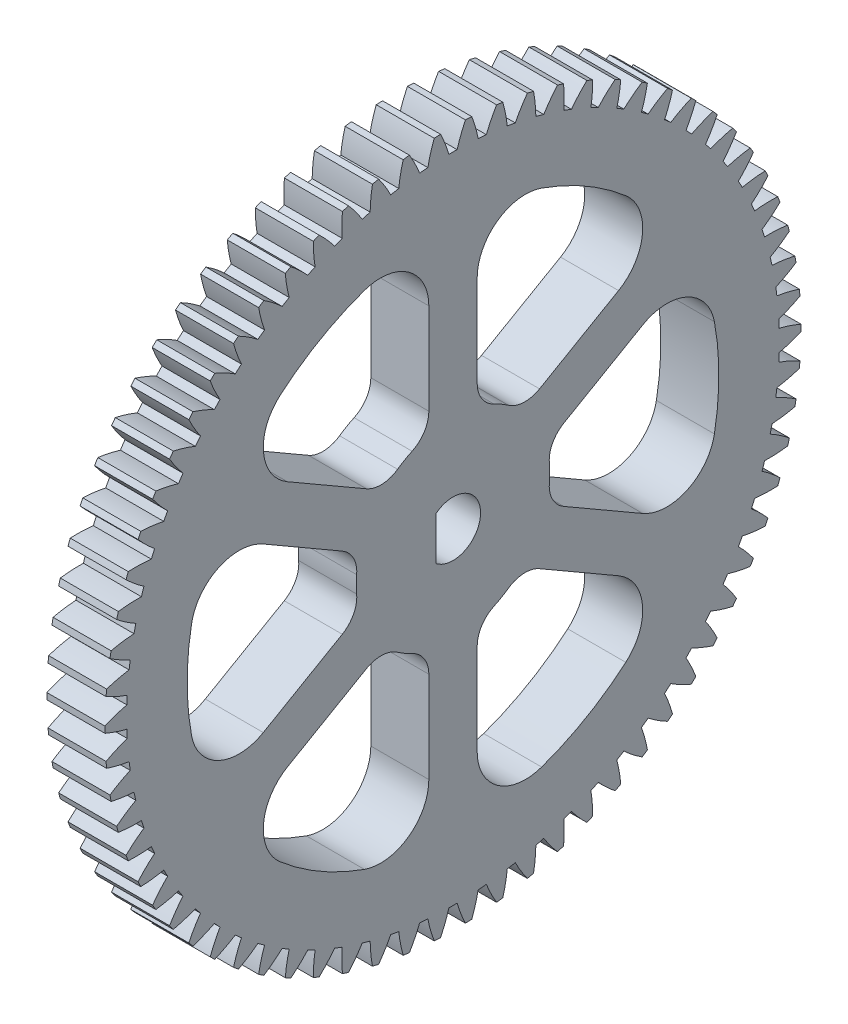
SolidWorks part; units mm, degrees
ref_plane "Plane1" through (0, 0, 0) normal (0, 0, 1) x (1, 0, 0)
ref_plane "Plane2" through (0, 0, 0) normal (0, 1, 0) x (1, 0, 0)
ref_plane "Plane3" through (0, 0, 0) normal (1, 0, 0) x (0, 0, -1)
sketch "HoldingSke" plane through (0, 0, 0) normal (0, 1, 0) x (1, 0, 0)
  line L0 (0, 0) -> (0.342, -0.9397)
  line L1 (-15, 0) -> (100, 0) construction
  line L2 (0, 0) -> (-2.1039, 2.3779)
  line L3 (0, 0) -> (-11.863, 4.5341)
  line L4 (0, 0) -> (2.9537, 8.1152)
  line L5 (0, 0) -> (-46.8476, -17.4728)
  line L6 (0, 0) -> (-4.9738, -3.3558)
  line L7 (-2.1039, 2.3779) -> (8.6587, 51.2065)
  line L8 (-76.2, 54.61) -> (-75.2, 54.61)
  line L9 (-71.009, 38.7566) -> (-53.1078, 45.2721)
  line L10 (-76.2, 71.12) -> (104.1128, 71.12)
  line L11 (0, 0) -> (-6, 0)
  line L12 (-76.2, 101.6) -> (-76.162, 101.6)
  line L13 (24.9733, 27.94) -> (52.9518, 28.4284)
  line L14 (24.9733, 27.94) -> (24.9743, 27.94)
  line L15 (24.9733, 27.94) -> (100.4006, 29.5858)
  line L16 (-63.627, -1) -> (-12.827, -1)
  circle A0 centre (0, 0) radius 3
  circle A1 centre (0, 0) radius 33.749
  circle A2 centre (0, 0) radius 37.5
  circle A3 centre (0, 0) radius 3
  dimension "MHD" = 67.498
  dimension "Hub_dia" = 75
  dimension "Bore" = 6
  dimension "MBD" = 6
  dimension "Num_teeth" = 70
  dimension "Pitch" = 1
  dimension "Overall_len" = 50
  dimension "Show_teeth" = 70
  dimension "Thickness" = 6
  dimension "OAL" = 50.0007
  dimension "T_dim" = 1
  dimension "Ap" = 20
  dimension "H" = 19.05
  dimension "Pitch_radius" = 180.3128
  dimension "Width" = 6
  dimension "Backlash" = 0.038
  dimension "Addendum_fac" = 1
  dimension "Dedendum_fac" = 1.25
  dimension "Clearance_fac" = 0.25
  dimension "Dedendum_add" = 0.001
  dimension "Module" = 1
sketch "BasProSke" plane through (0, 0, 0) normal (0, 1, 0) x (1, 0, 0)
  line L0 (-10, 0) -> (60, 0) construction
  line L1 (0, 0) -> (0, 36)
  line L2 (0, 0) -> (6, 0)
  line L3 (6, 0) -> (6, 36)
  line L4 (6, 36) -> (0, 36)
  dimension "Thickness" = 6
  dimension "Diameter" = 72
revolve "Base-Revolve" add sketch "BasProSke" angle 360 about L0
sketch "TooCutSke" plane through (0, 0, 0) normal (1, 0, 0) x (0, 0, -1)
  line L1 (0, 0) -> (0, 107) construction
  line L2 (0, 0) -> (-0.8518, 34.9896) construction
  line L3 (0, 0) -> (-3.1399, 69.9148) construction
  line L4 (-0.8518, 34.9896) -> (-1.5699, 34.9574) construction
  arc A0 (0.4247, 33.7463) -> (-0.4247, 33.7463) centre (0, 0) ccw
  arc A1 (1.3008, 36.0019) -> (-1.3008, 36.0019) centre (0, 0) ccw
  circle A2 centre (0, 0) radius 35 construction
  circle A3 centre (0, 0) radius 32.8892 construction
  arc A4 (-0.4247, 33.7463) -> (-1.3008, 36.0019) centre (-13.8641, 29.8243) ccw
  arc A5 (1.3008, 36.0019) -> (0.4247, 33.7463) centre (13.8641, 29.8243) ccw
  dimension "Root_dia" = 67.498
  dimension "Overcut_dia" = 72.0508
  dimension "Pitch_dia" = 70
  dimension "Base_dia" = 65.7785
  dimension "Flank_rad" = 14
  dimension "Half_ang" = 2.571
  dimension "Half_CT" = 0.7188
extrude "ToothCut" cut sketch "TooCutSke" along normal through all
fillet "Breaks" [suppressed] radius 0.02
fillet "RootFillets" [suppressed] radius 0.251
pattern_circular "TeethCuts" count 70 every 5.143 about axis through (-10, 0, 0) along (1, 0, 0) of "ToothCut", "RootFillets", "Breaks"
sketch "HubNeaOneSke" plane through (0, 0, 0) normal (-1, 0, 0) x (0, 0, 1)
  circle A0 centre (0, 0) radius 33.749
  dimension "Diameter" = 67.498
extrude "HubNearOne" [suppressed] add sketch "HubNeaOneSke" along normal blind 44.0007
sketch "HubNeaBotSke" plane through (0, 0, 0) normal (-1, 0, 0) x (0, 0, 1)
  circle A0 centre (0, 0) radius 33.749
  dimension "Diameter" = 67.498
extrude "HubNearBoth" [suppressed] add sketch "HubNeaBotSke" along normal blind 22.0004
ref_plane "FarPln" through (6, 0, 0) normal (1, 0, 0) x (0, 0, -1)
sketch "HubFarSke" plane through (6, 0, 0) normal (1, 0, 0) x (0, 0, -1)
  circle A0 centre (0, 0) radius 33.749
  dimension "Diameter" = 67.498
extrude "HubFar" [suppressed] add sketch "HubFarSke" along normal blind 22.0004
sketch "KeySke" plane through (0, 0, 0) normal (1, 0, 0) x (0, 0, -1)
  line L0 (-1, 0) -> (-1, 4)
  line L1 (-1, 4) -> (1, 4)
  line L2 (1, 4) -> (1, 0)
  line L3 (0, 0) -> (0, 34) construction
  line L4 (-1, 0) -> (1, 0)
  dimension "Offset" = 4
  dimension "Width" = 2
extrude "Keyway" [suppressed] cut sketch "KeySke" along normal mid plane 100.0014
pattern_circular "Keyway2" [suppressed] count 2 every 90 about axis through (-10, 0, 0) along (1, 0, 0)
sketch "Sketch1" plane through (6, 0, 0) normal (1, 0, 0) x (0, 0, -1)
  line L0 (-1.7493, 2.25) -> (-1.7493, -2.25)
  arc A0 (-1.7493, -2.25) -> (-1.7493, 2.25) centre (0, 0) ccw
  dimension "D1" = 5.7
  dimension "D2" = 4.5
extrude "Cut-Extrude1" cut sketch "Sketch1" against normal through all
sketch "Sketch2" plane through (6, 0, 0) normal (1, 0, 0) x (0, 0, -1)
  line L0 (-2.5, 27.3861) -> (-2.5, 9.6825)
  line L1 (-7.1353, 7.0063) -> (-22.4671, 15.8581)
  arc A1 (-2.5, 9.6825) -> (-7.1353, 7.0063) centre (0, 0) ccw
  arc A2 (-2.5, 27.3861) -> (-22.4671, 15.8581) centre (0, 0) ccw
  dimension "D2" = 20
  dimension "D3" = 55
  dimension "D4" = 2.5
  dimension "D5" = 2.5
  dimension "D6" = 60
extrude "Cut-Extrude2" cut sketch "Sketch2" against normal through all
fillet "Fillet1" radius 5 2 edges at (3, 15.8581, 22.4671) (3, 27.3861, 2.5)
fillet "Fillet2" radius 3 2 edges at (3, 7.0063, 7.1353) (3, 9.6825, 2.5)
pattern_circular "CirPattern1" count 6 every 60 about axis through (0, 0, 0) along (1, 0, 0) of "Fillet1", "Cut-Extrude2", "Fillet2"
equation "' \"Module@HoldingSke\" = 6.35"
equation "' \"Num_teeth@HoldingSke\" = 12"
equation "' \"Ap@HoldingSke\" =  20"
equation "' \"Ap@HoldingSke\" = 20"
equation "' \"Width@HoldingSke\" = 0.5 * 25.4"
equation "' \"Hub_dia@HoldingSke\"= 1 * 25.4"
equation "' \"Hub_dia@HoldingSke\" = 1 * 25.4"
equation "' \"Overall_len@HoldingSke\" = 1.0 * 25.4"
equation "' \"Bore@HoldingSke\" = 0.75 * 25.4"
equation "' \"T_dim@HoldingSke\" = 0.1 * 25.4"
equation "' \"Width@KeySke\" = 0.25 * 25.4"
equation "' \"Show_teeth@HoldingSke\" = 13"
equation "' \"Backlash@HoldingSke\" = 0.009 * 25.4"
equation "' \"Addendum_fac@HoldingSke\" = 1.0"
equation "' \"Dedendum_fac@HoldingSke\" = 1.25"
equation "' \"Dedendum_add@HoldingSke\" = 0.00005 * 25.4"
equation "' \"Clearance_fac@HoldingSke\" = 0.25"
equation "\"Pitch@HoldingSke\" = 1 / \"Module@HoldingSke\""
equation "\"Overcut_dia@TooCutSke\" = (\"Num_teeth@HoldingSke\" + 2 * \"Addendum_fac@HoldingSke\") / \"Pitch@HoldingSke\" + 0.002 * 25.4"
equation "\"Pitch_dia@TooCutSke\" = \"Num_teeth@HoldingSke\" / \"Pitch@HoldingSke\""
equation "\"Base_dia@TooCutSke\" = \"Num_teeth@HoldingSke\" / \"Pitch@HoldingSke\" * cos((\"Ap@HoldingSke\"  * 3.14159265 / 180))"
equation "\"Root_dia@TooCutSke\" = (\"Num_teeth@HoldingSke\" + 2) / \"Pitch@HoldingSke\" - 2 * (\"Addendum_fac@HoldingSke\" + \"Dedendum_fac@HoldingSke\") / \"Pitch@HoldingSke\" - \"Dedendum_add@HoldingSke\" * 2"
equation "\"Half_ang@TooCutSke\" = 180 / \"Num_teeth@HoldingSke\""
equation "\"Half_CT@TooCutSke\" = \"Num_teeth@HoldingSke\" / \"Pitch@HoldingSke\" * sin((3.14159265 / 2 / \"Num_teeth@HoldingSke\")) / 2 - 7 * \"Backlash@HoldingSke\" / 4"
equation "\"Flank_rad@TooCutSke\" = \"Num_teeth@HoldingSke\" / \"Pitch@HoldingSke\" / 5"
equation "\"Radius@RootFillets\" = \"Clearance_fac@HoldingSke\" / \"Pitch@HoldingSke\" + \"Dedendum_add@HoldingSke\""
equation "\"Break_rad@Breaks\" = 0.02 / \"Pitch@HoldingSke\""
equation "\"Thickness@HoldingSke\" = \"Width@HoldingSke\""
equation "\"OAL@HoldingSke\" = \"Thickness@HoldingSke\""
equation "\"MHD@HoldingSke\" = (\"Num_teeth@HoldingSke\" + 2) / \"Pitch@HoldingSke\" - 2 * (\"Addendum_fac@HoldingSke\" + \"Dedendum_fac@HoldingSke\")  / \"Pitch@HoldingSke\" - \"Dedendum_add@HoldingSke\" * 2"
equation "\"MBD@HoldingSke\" = (\"Num_teeth@HoldingSke\" + 2) / \"Pitch@HoldingSke\" - 2 * (\"Addendum_fac@HoldingSke\" + \"Dedendum_fac@HoldingSke\")  / \"Pitch@HoldingSke\" - \"Dedendum_add@HoldingSke\" * 2 - 0.002 * 25.4"
equation "\"MHD@HoldingSke\" = ((sgn( \"MHD@HoldingSke\" - \"Hub_dia@HoldingSke\" )-1)*( \"MHD@HoldingSke\" - \"Hub_dia@HoldingSke\" ))/-2+ \"Hub_dia@HoldingSke\""
equation "\"MBD@HoldingSke\" = ((sgn( \"MBD@HoldingSke\" - \"Bore@HoldingSke\" )-1)*( \"MBD@HoldingSke\" - \"Bore@HoldingSke\" ))/-2+ \"Bore@HoldingSke\""
equation "\"OAL@HoldingSke\" = ((sgn( \"OAL@HoldingSke\" - \"Overall_len@HoldingSke\" )+1)*( \"OAL@HoldingSke\" - \"Overall_len@HoldingSke\" ))/2 + \"Overall_len@HoldingSke\" + 0.000002 * 25.4"
equation "\"Num_teeth@TeethCuts\" = int( \"Show_teeth@HoldingSke\" ) + 1"
equation "\"Num_teeth@TeethCuts\" = ((sgn( \"Num_teeth@TeethCuts\" - \"Num_teeth@HoldingSke\" )-1)*( \"Num_teeth@TeethCuts\" - \"Num_teeth@HoldingSke\" ))/-2+ \"Num_teeth@HoldingSke\""
equation "\"Num_teeth@TeethCuts\" = ((sgn( \"Num_teeth@TeethCuts\" - 2.0)+1)*( \"Num_teeth@TeethCuts\" - 2.0))/2 +2.0"
equation "\"Angle@TeethCuts\" = 360.0 / \"Num_teeth@HoldingSke\""
equation "\"Diameter@BasProSke\" = (\"Num_teeth@HoldingSke\" + 2 * \"Addendum_fac@HoldingSke\") / \"Pitch@HoldingSke\""
equation "\"Thickness@BasProSke\"  = \"Thickness@HoldingSke\""
equation "' \"Fillet_rad@BasProSke\" =  \"Thickness@HoldingSke\" * 0.05"
equation "' \"Fillet_rad@BasProSke\" = \"Thickness@HoldingSke\" * 0.05"
equation "\"MHD@HoldingSke\" = ((sgn( \"MHD@HoldingSke\" - \"Root_dia@TooCutSke\" )-1)*( \"MHD@HoldingSke\" - \"Root_dia@TooCutSke\" ))/-2+ \"Root_dia@TooCutSke\""
equation "\"Diameter@HubNeaOneSke\" = \"MHD@HoldingSke\""
equation "\"Length@HubNearOne\" = \"OAL@HoldingSke\" - \"Thickness@BasProSke\""
equation "\"Diameter@HubNeaBotSke\" = \"MHD@HoldingSke\""
equation "\"Length@HubNearBoth\" = ( \"OAL@HoldingSke\" - \"Thickness@BasProSke\" ) / 2.0"
equation "\"Thickness@FarPln\" = \"Thickness@BasProSke\""
equation "\"Diameter@HubFarSke\" = \"MHD@HoldingSke\""
equation "\"Length@HubFar\" = ( \"OAL@HoldingSke\" - \"Thickness@BasProSke\" ) / 2.0"
equation "\"D1@Keyway\" = \"OAL@HoldingSke\" * 2.0"
equation "\"Offset@KeySke\" = \"T_dim@HoldingSke\" + \"MBD@HoldingSke\" / 2.0"
